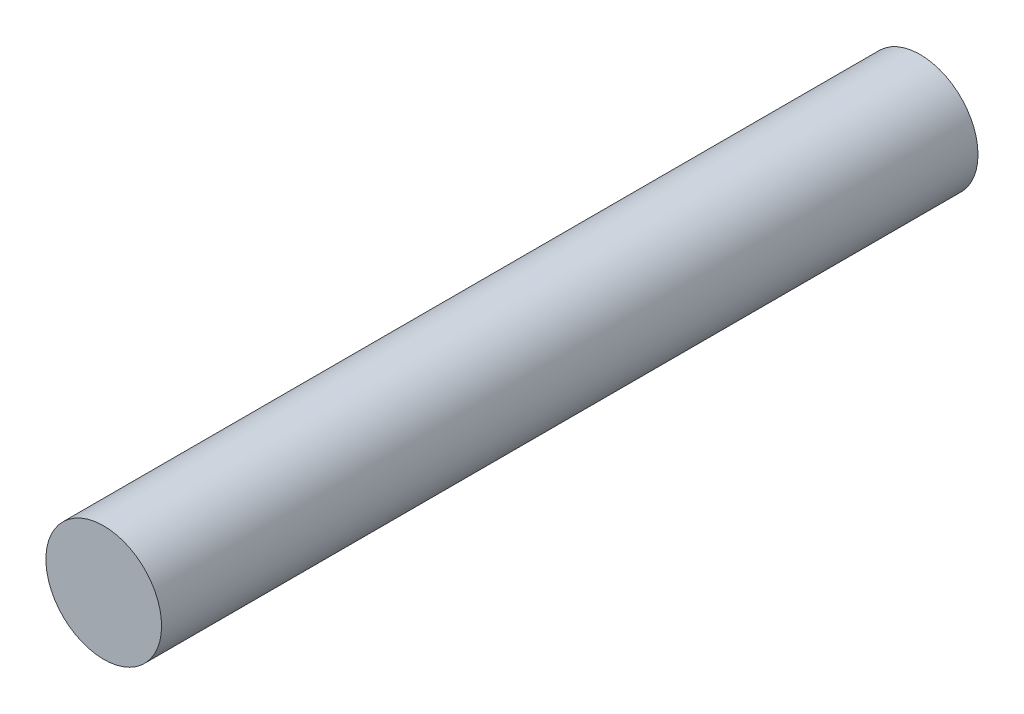
SolidWorks part; units mm, degrees
ref_plane "Front Plane" through (0, 0, 0) normal (0, 0, 1) x (1, 0, 0)
ref_plane "Top Plane" through (0, 0, 0) normal (0, 1, 0) x (1, 0, 0)
ref_plane "Right Plane" through (0, 0, 0) normal (1, 0, 0) x (0, 0, -1)
sketch "Sketch1" plane through (0, 0, 0) normal (0, 0, 1) x (1, 0, 0)
  circle A0 centre (0, 0) radius 8.5
  dimension "D1" = 17
extrude "Boss-Extrude1" add sketch "Sketch1" along normal mid plane 120
